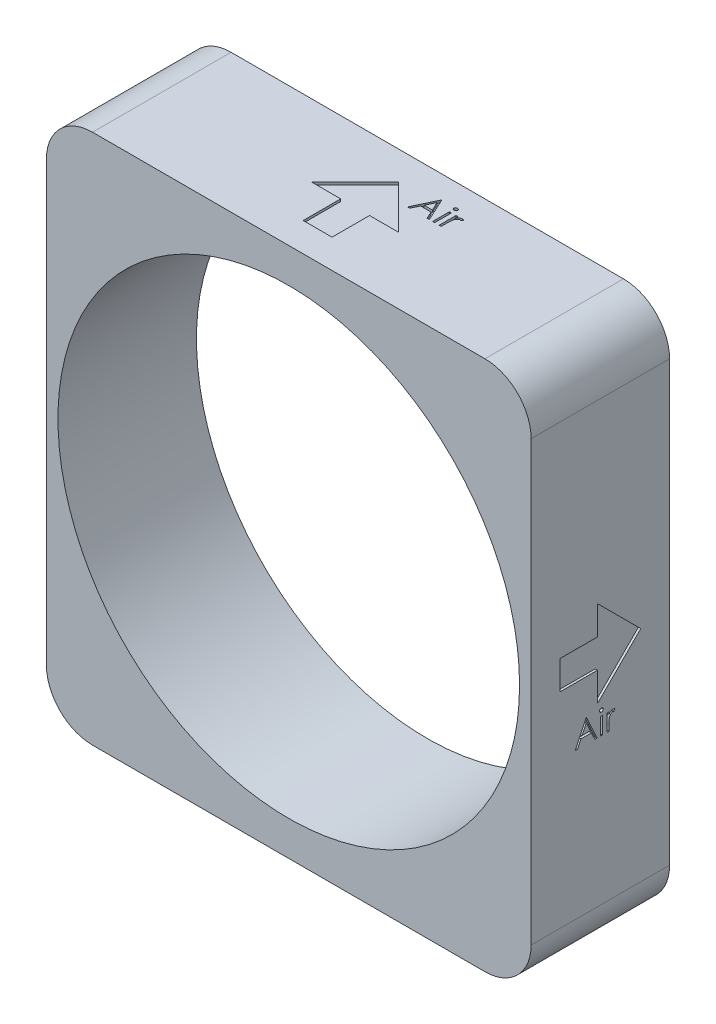
SolidWorks part; units mm, degrees
material "1023 Carbon Steel Sheet (SS)"
ref_plane "Front Plane" through (0, 0, 0) normal (0, 0, 1) x (1, 0, 0)
ref_plane "Top Plane" through (0, 0, 0) normal (0, 1, 0) x (1, 0, 0)
ref_plane "Right Plane" through (0, 0, 0) normal (1, 0, 0) x (0, 0, -1)
sketch "Sketch1" plane through (0, 0, 0) normal (0, 0, 1) x (1, 0, 0)
  line L1 (-266.7, -292.1) -> (266.7, -292.1)
  line L2 (-266.7, -292.1) -> (-266.7, 292.1)
  line L3 (-266.7, 292.1) -> (266.7, 292.1)
  line L4 (266.7, -292.1) -> (266.7, 292.1)
  line L5 (-266.7, -292.1) -> (266.7, 292.1) construction
  line L6 (-266.7, 292.1) -> (266.7, -292.1) construction
  point P0 (0, 0)
  dimension "D1" = 584.2
  dimension "D2" = 533.4
extrude "Boss-Extrude1" add sketch "Sketch1" along normal blind 152.4
sketch "Sketch2" plane through (0, 0, 152.4) normal (0, 0, 1) x (1, 0, 0)
  circle A0 centre (0, 0) radius 254
  dimension "D1" = 508
extrude "Cut-Extrude1" cut sketch "Sketch2" against normal through all contours A0
fillet "Fillet1" radius 50.8 4 edges at (266.7, -292.1, 76.2) (266.7, 292.1, 76.2) (-266.7, -292.1, 76.2) (-266.7, 292.1, 76.2)
sketch "Sketch3" plane through (266.7, 0, 0) normal (1, 0, 0) x (0, 0, -1)
  line L7 (-120.65, 0) -> (-31.75, 0) construction
  line L8 (-152.4, 0) -> (0, 0) construction
  line L9 (-152.4, -241.3) -> (-152.4, 241.3) construction
  line L10 (-120.65, 15.875) -> (-120.65, -15.875)
  line L11 (-120.65, -15.875) -> (-79.375, -15.875)
  line L12 (-79.375, -15.875) -> (-79.375, -47.625)
  line L13 (-79.375, -47.625) -> (-31.75, 0)
  line L14 (-31.75, 0) -> (-79.375, 47.625)
  line L15 (-79.375, 47.625) -> (-79.375, 15.875)
  line L16 (-79.375, 15.875) -> (-120.65, 15.875)
  line L17 (-79.375, 15.875) -> (-79.375, -15.875) construction
  text T0 "Air\r\n" font "Century Gothic" height 25.4
  point P1 (0, 0)
  point P2 (-229.0328, 56.7545)
  point P3 (-76.2, 0)
  point P4 (-76.2, 0)
  dimension "D1" = 31.75
  dimension "D2" = 88.9
extrude "Cut-Extrude2" cut sketch "Sketch3" against normal blind 2.54
sketch "Sketch4" plane through (0, 292.1, 0) normal (0, 1, 0) x (1, 0, 0)
  line L7 (0, -120.65) -> (0, -31.75) construction
  line L8 (0, -152.4) -> (0, 0) construction
  line L10 (-15.875, -120.65) -> (15.875, -120.65)
  line L11 (15.875, -120.65) -> (15.875, -79.375)
  line L12 (15.875, -79.375) -> (47.625, -79.375)
  line L13 (47.625, -79.375) -> (0, -31.75)
  line L14 (0, -31.75) -> (-47.625, -79.375)
  line L15 (-47.625, -79.375) -> (-15.875, -79.375)
  line L16 (-15.875, -79.375) -> (-15.875, -120.65)
  line L17 (-15.875, -79.375) -> (15.875, -79.375) construction
  line L18 (215.9, -152.4) -> (-215.9, -152.4) construction
  text T0 "Air\r\n" font "Century Gothic" height 25.4
  point P1 (-7.6367, -64.092)
  point P2 (-236.6694, -7.3375)
  point P3 (0, -76.2)
  point P4 (0, -76.2)
  point P6 (0, 0)
  point P7 (-204.4692, 0)
  point P10 (-104.5554, 0)
  point P15 (-47.2495, -111.523)
  point P16 (-22.9388, -52.0036)
  point P22 (-149.5223, -25.178)
  point P23 (-153.4992, 0)
  point P24 (-161.5255, 0)
  point P25 (-2.085, -94.3862)
  point P26 (0, -152.4)
  dimension "D1" = 31.75
  dimension "D2" = 88.9
extrude "Cut-Extrude3" cut sketch "Sketch4" against normal blind 2.54
sketch "Sketch7" plane through (-266.7, 0, 0) normal (-1, 0, 0) x (0, 0, 1)
  line L0 (120.65, 0) -> (31.75, 0) construction
  line L1 (152.4, 0) -> (0, 0) construction
  line L2 (120.65, -15.875) -> (120.65, 15.875)
  line L3 (120.65, 15.875) -> (79.375, 15.875)
  line L4 (79.375, 15.875) -> (79.375, 47.625)
  line L5 (79.375, 47.625) -> (31.75, 0)
  line L6 (31.75, 0) -> (79.375, -47.625)
  line L7 (79.375, -47.625) -> (79.375, -15.875)
  line L8 (79.375, -15.875) -> (120.65, -15.875)
  line L9 (79.375, -15.875) -> (79.375, 15.875) construction
  line L10 (152.4, 241.3) -> (152.4, -241.3) construction
  text T0 "Air\r\n" font "Century Gothic" height 25.4
  point P1 (76.2, 0)
  point P2 (76.2, 0)
  point P12 (0, 0)
  point P14 (152.4, 0)
  point P18 (-15.5505, 0)
  point P19 (-15.5505, 0)
  dimension "D1" = 31.75
  dimension "D2" = 88.9
extrude "Cut-Extrude4" cut sketch "Sketch7" against normal blind 2.54 contours L6 L7 L8 L2 L3 L4 L5
